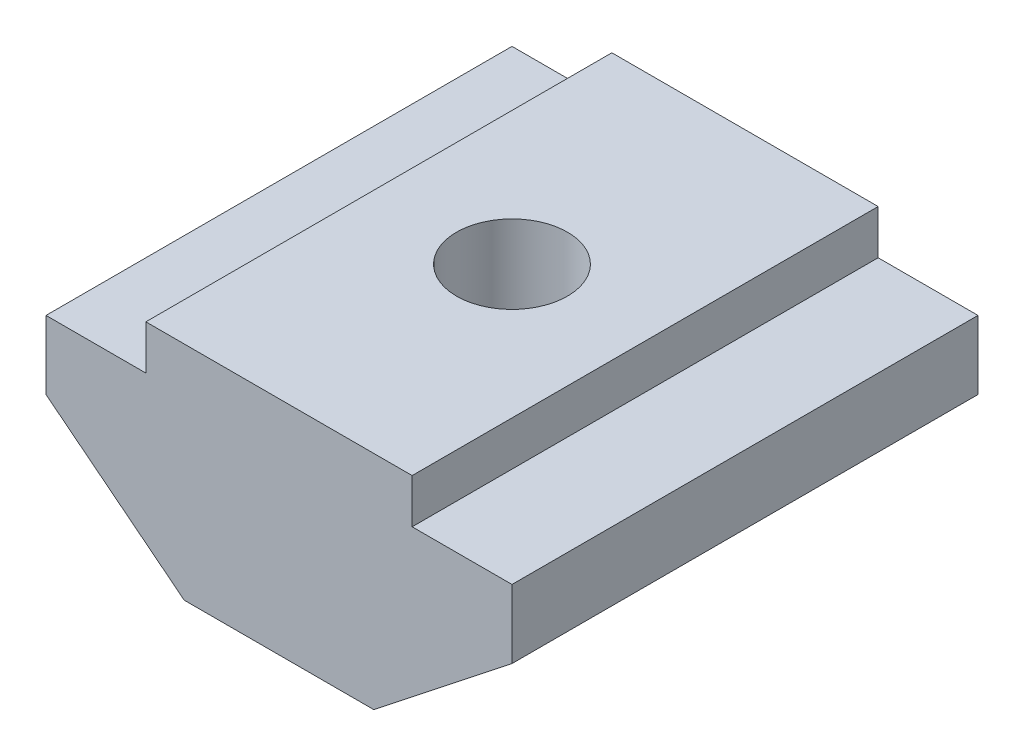
SolidWorks part; units mm, degrees
ref_plane "Front" through (0, 0, 0) normal (0, 0, 1) x (1, 0, 0)
ref_plane "Top" through (0, 0, 0) normal (0, 1, 0) x (1, 0, 0)
ref_plane "Right" through (0, 0, 0) normal (1, 0, 0) x (0, 0, -1)
sketch "Sketch1" plane through (0, 0, 0) normal (0, 0, 1) x (1, 0, 0)
  line L0 (0, 0) -> (0, 5) construction
  line L1 (-3, 5) -> (3, 5)
  line L2 (3, 5) -> (3, 4)
  line L3 (3, 4) -> (5.25, 4)
  line L4 (5.25, 4) -> (5.25, 2.4559)
  line L5 (5.25, 2.4559) -> (2.1356, 0)
  line L6 (2.1356, 0) -> (-2.1356, 0)
  line L7 (-5.25, 2.4559) -> (-2.1356, 0)
  line L8 (-5.25, 4) -> (-5.25, 2.4559)
  line L9 (-3, 4) -> (-5.25, 4)
  line L10 (-3, 5) -> (-3, 4)
  dimension "D1" = 1
  dimension "D2" = 6
  dimension "D3" = 5
  dimension "D4" = 10.5
extrude "Boss-Extrude1" add sketch "Sketch1" along normal blind 10.5
hole_wizard "M3x0.5 Tapped Hole1" positions "Sketch2" profile "Sketch3" tap size "M3x0.5" standard "ANSI Metric" end condition through all
sketch "Sketch2" plane through (0, 5, 0) normal (0, 1, 0) x (1, 0, 0)
  line L0 (0, 0) -> (0, -10.5) construction
  line L1 (3, -10.5) -> (-3, -10.5) construction
  point P0 (0, -5.25)
  point P12 (0, -5.25)
sketch "Sketch3" plane through (0, 5, 5.25) normal (1, 0, 0) x (0, 0, 1)
  line L0 (0, 0) -> (0, 5)
  line L1 (0, 5) -> (1.25, 5)
  line L2 (1.25, 5) -> (1.25, 0)
  line L5 (1.25, 0) -> (0, 0)
  line L11 (0, -6.35) -> (0, 107.95) construction
  dimension "Thru Tap Drill Dia." = 2.5
  dimension "Thru Tap Drill Depth" = 5
cosmetic thread "Hole Thread1"
